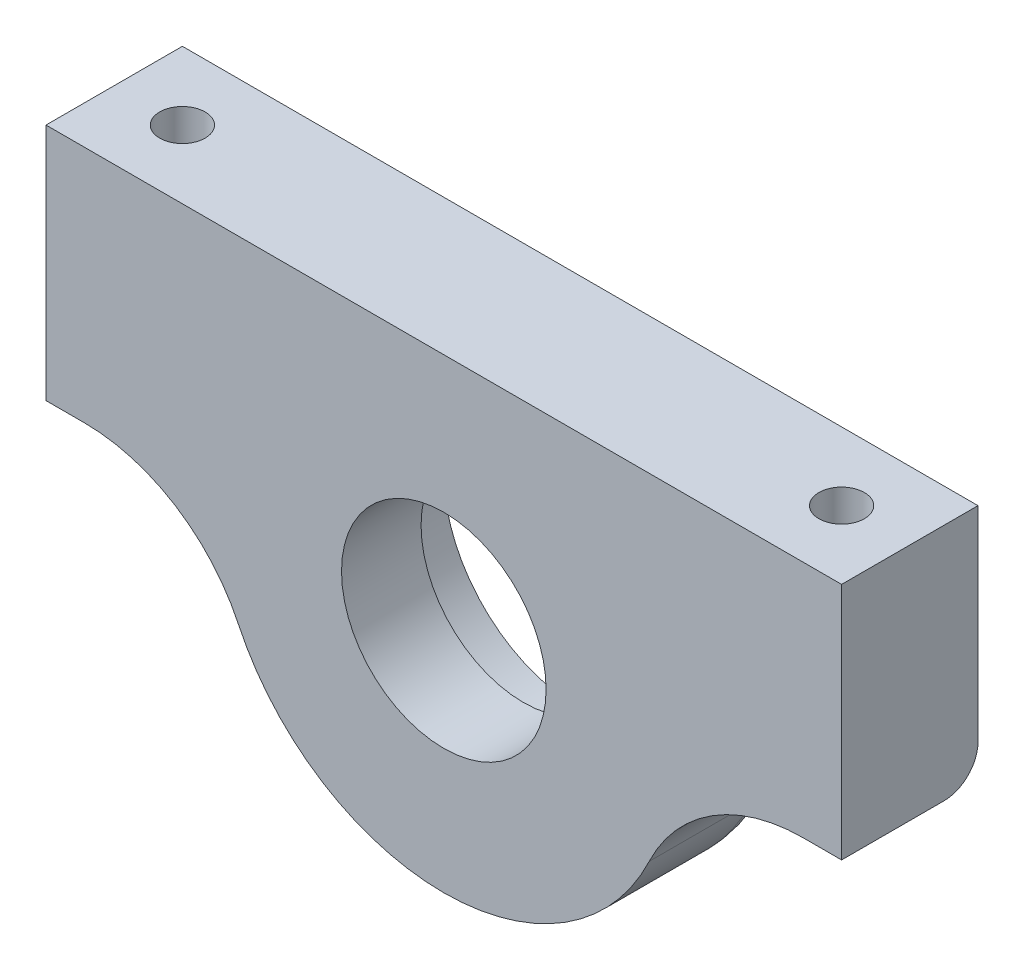
SolidWorks part; units mm, degrees
ref_plane "Front Plane" through (0, 0, 0) normal (0, 0, 1) x (1, 0, 0)
ref_plane "Top Plane" through (0, 0, 0) normal (0, 1, 0) x (1, 0, 0)
ref_plane "Right Plane" through (0, 0, 0) normal (1, 0, 0) x (0, 0, -1)
sketch "Sketch1" plane through (0, 0, 0) normal (0, 0, 1) x (1, 0, 0)
  line L0 (-35, 21) -> (35, 21)
  line L1 (0, 0) -> (0, 21) construction
  line L2 (-35, 21) -> (-35, 0)
  line L3 (-35, 0) -> (-31.6228, 0)
  line L4 (35, 0) -> (35, 21)
  line L5 (-20, 0) -> (20, 0) construction
  line L6 (31.6228, 0) -> (35, 0)
  circle A0 centre (0, 0) radius 9
  arc A1 (-18.0702, -8.5714) -> (18.0702, -8.5714) centre (0, 0) ccw
  arc A2 (-18.0702, -8.5714) -> (-31.6228, 0) centre (-31.6228, -15) ccw
  arc A3 (18.0702, -8.5714) -> (31.6228, 0) centre (31.6228, -15) cw
  dimension "D1" = 40
  dimension "D2" = 18
  dimension "D5" = 15
  dimension "D3" = 70
  dimension "D4" = 21
extrude "Boss-Extrude1" add sketch "Sketch1" along normal mid plane 12
sketch "Sketch2" plane through (0, 0, -6) normal (0, 0, -1) x (-1, 0, 0)
  circle A0 centre (0, 0) radius 12
  dimension "D1" = 24
extrude "Cut-Extrude1" cut sketch "Sketch2" against normal blind 5
sketch "Sketch3" plane through (0, 21, 0) normal (0, 1, 0) x (1, 0, 0)
  line L0 (-35, 0) -> (-29, 0) construction
  line L3 (-35, -6) -> (-35, 6) construction
  line L4 (-29, 0) -> (29, 0) construction
  line L5 (29, 0) -> (35, 0) construction
  line L6 (35, -6) -> (35, 6) construction
  circle A0 centre (-29, 0) radius 2
  circle A1 centre (29, 0) radius 2
  dimension "D1" = 4
  dimension "D2" = 58
extrude "Cut-Extrude2" cut sketch "Sketch3" against normal blind 10
fillet "Fillet1" radius 3 5 edges at (-33.3114, 0, -6) (-23.6049, -2.3227, -6) (33.3114, 0, -6) (23.6049, -2.3227, -6) (0, -20, -6)
